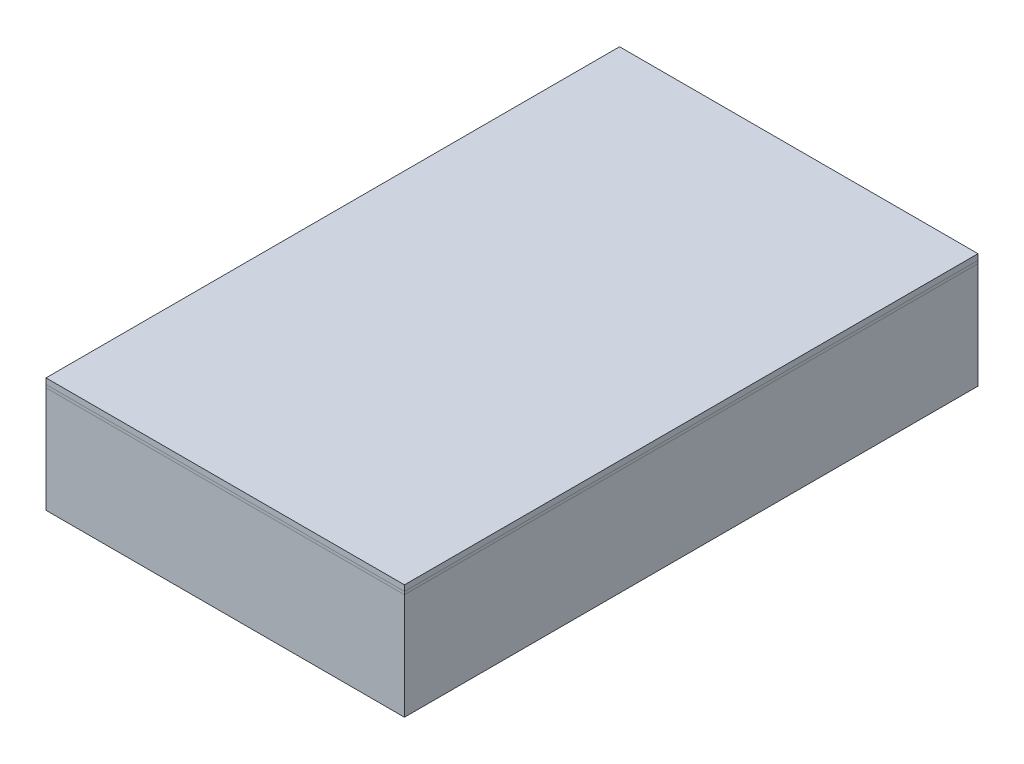
SolidWorks part; units mm, degrees
ref_plane "Front Plane" through (0, 0, 0) normal (0, 0, 1) x (1, 0, 0)
ref_plane "Top Plane" through (0, 0, 0) normal (0, 1, 0) x (1, 0, 0)
ref_plane "Right Plane" through (0, 0, 0) normal (1, 0, 0) x (0, 0, -1)
sketch "Sketch1" plane through (0, 0, 0) normal (0, 1, 0) x (1, 0, 0)
  line L1 (-0.625, -1) -> (0.625, -1)
  line L2 (-0.625, -1) -> (-0.625, 1)
  line L3 (-0.625, 1) -> (0.625, 1)
  line L4 (0.625, -1) -> (0.625, 1)
  line L5 (-0.625, -1) -> (0.625, 1) construction
  line L6 (-0.625, 1) -> (0.625, -1) construction
  point P0 (0, 0)
  dimension "D1" = 1.25
  dimension "D2" = 2
extrude "Boss-Extrude1" add sketch "Sketch1" along normal blind 0.37
sketch "Sketch2" plane through (0, 0.37, 0) normal (0, 1, 0) x (1, 0, 0)
  line L1 (-0.625, -1) -> (0.625, -1)
  line L2 (-0.625, -1) -> (-0.625, 1)
  line L3 (-0.625, 1) -> (0.625, 1)
  line L4 (0.625, -1) -> (0.625, 1)
extrude "Boss-Extrude2" add sketch "Sketch2" along normal blind 0.01 separate body
sketch "Sketch3" plane through (0, 0.38, 0) normal (0, 1, 0) x (1, 0, 0)
  line L1 (-0.625, 1) -> (0.625, 1)
  line L2 (-0.625, 1) -> (-0.625, -1)
  line L3 (-0.625, -1) -> (0.625, -1)
  line L4 (0.625, 1) -> (0.625, -1)
extrude "Boss-Extrude3" add sketch "Sketch3" along normal blind 0.02 separate body
